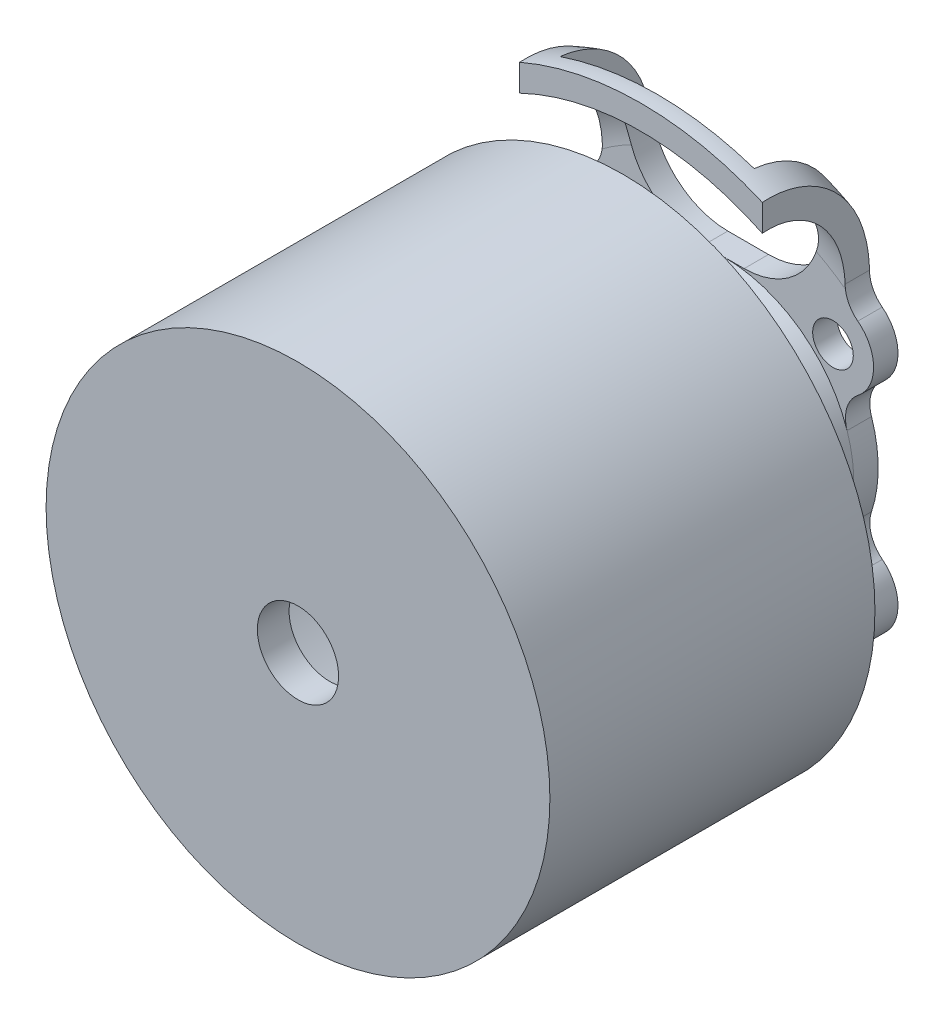
SolidWorks part; units mm, degrees
material "AISI 1020 Steel, Cold Rolled"
ref_plane "Front Plane" through (0, 0, 0) normal (0, 0, 1) x (1, 0, 0)
ref_plane "Top Plane" through (0, 0, 0) normal (0, 1, 0) x (1, 0, 0)
ref_plane "Right Plane" through (0, 0, 0) normal (1, 0, 0) x (0, 0, -1)
sketch "Sketch1" plane through (0, 0, 0) normal (1, 0, 0) x (0, 0, -1)
  line L1 (0, 15.5) -> (20, 15.5)
  line L3 (20, 0) -> (0, 0) construction
  line L4 (20, 2.5) -> (0, 2.5) construction
  line L5 (0, 15.5) -> (0, 2.5)
  line L6 (0, 2.5) -> (1.95, 2.5)
  line L7 (1.95, 2.5) -> (1.95, 13.5)
  line L8 (1.95, 13.5) -> (18.05, 13.5)
  line L9 (18.05, 13.5) -> (18.05, 2.5)
  line L10 (18.05, 2.5) -> (20, 2.5)
  line L11 (20, 6.5) -> (20, 15.5)
  line L12 (20, 2.5) -> (27.7, 2.5)
  line L13 (27.7, 2.5) -> (27.7, 12.5)
  line L14 (27.7, 18.75) -> (-25.5, 18.75) construction
  line L18 (20, 6.5) -> (26.2, 8)
  line L19 (26.2, 8) -> (26.2, 12.5)
  line L20 (21.1007, 18.7402) -> (21.1007, 17.2402)
  line L21 (26.2, 8) -> (27.7, 8) construction
  line L22 (10, 13.5) -> (10, 15.5) construction
  arc A2 (27.7, 12.5) -> (21.1007, 18.7402) centre (21.45, 12.5) ccw
  arc A3 (26.2, 12.5) -> (21.1007, 17.2402) centre (21.4471, 12.5) ccw
  dimension "D10" = 1.5
  dimension "D1" = 20
  dimension "D2" = 15.5
  dimension "D3" = 2.5
  dimension "D4" = 12.5
  dimension "D5" = 27.7
  dimension "D6" = 18.75
  dimension "D7" = 53.2
  dimension "D8" = 6.5
  dimension "D9" = 8
  dimension "D11" = 16.1
  dimension "D12" = 11
revolve "Revolve1" add sketch "Sketch1" angle 360 about L3
sketch "Sketch2" plane through (0, 0, -27.7) normal (0, 0, -1) x (-1, 0, 0)
  line L0 (-5.9675, 23.4161) -> (-5.9675, 12.7175)
  line L1 (-6.7175, -6.7175) -> (6.7175, -6.7175) construction
  line L2 (-6.7175, -6.7175) -> (-6.7175, 6.7175) construction
  line L3 (-6.7175, 6.7175) -> (6.7175, 6.7175) construction
  line L4 (6.7175, -6.7175) -> (6.7175, 6.7175) construction
  line L5 (-6.7175, -6.7175) -> (6.7175, 6.7175) construction
  line L6 (-6.7175, 6.7175) -> (6.7175, -6.7175) construction
  line L7 (-5.9675, 23.4161) -> (5.9675, 23.4161)
  line L8 (5.9675, 23.4161) -> (5.9675, 12.7175)
  line L9 (0, 0) -> (0, 23.4161) construction
  line L10 (1.25, 8) -> (-1.25, 8)
  line L11 (-7.4675, 23.4161) -> (-7.4675, 10.2795)
  line L12 (7.4675, 23.4161) -> (7.4675, 10.2795)
  line L13 (7.4675, 23.4161) -> (5.9675, 23.4161) construction
  line L14 (6.7175, 6.7175) -> (6.7175, 23.4161) construction
  line L15 (-5.9675, 23.4161) -> (-7.4675, 23.4161) construction
  circle A0 centre (0, 0) radius 9.5 construction
  circle A1 centre (0, 0) radius 8 construction
  circle A2 centre (0, 0) radius 12.5 construction
  circle A3 centre (-6.7175, 6.7175) radius 1.25
  circle A4 centre (6.7175, 6.7175) radius 1.25
  circle A5 centre (6.7175, -6.7175) radius 1.25
  circle A6 centre (-6.7175, -6.7175) radius 1.25
  circle A7 centre (6.7175, 6.7175) radius 2.5 construction
  circle A8 centre (6.7175, -6.7175) radius 2.5 construction
  circle A9 centre (-6.7175, -6.7175) radius 2.5 construction
  circle A11 centre (-6.7175, 6.7175) radius 2.5 construction
  arc A17 (-5.9675, 12.7175) -> (-1.25, 8) centre (-1.25, 12.7175) ccw
  arc A19 (5.9675, 12.7175) -> (1.25, 8) centre (1.25, 12.7175) cw
  arc A22 (-7.4675, 23.4161) -> (7.4675, 23.4161) centre (0, -0.8704) ccw
  arc A25 (8.2453, 8.6964) -> (8.2548, 4.746) centre (6.7175, 6.7175) cw
  arc A26 (7.5877, 2.5351) -> (7.5877, -2.5351) centre (0, 0) cw
  arc A27 (8.2548, -4.746) -> (4.746, -8.2548) centre (6.7175, -6.7175) cw
  arc A28 (2.5351, -7.5877) -> (-2.5351, -7.5877) centre (0, 0) cw
  arc A29 (-4.746, -8.2548) -> (-8.2548, -4.746) centre (-6.7175, -6.7175) cw
  arc A30 (-8.2453, 8.6964) -> (-8.2548, 4.746) centre (-6.7175, 6.7175) ccw
  arc A31 (-7.5877, 2.5351) -> (-7.5877, -2.5351) centre (0, 0) ccw
  arc A32 (-8.2453, 8.6964) -> (-7.4675, 10.2795) centre (-9.4675, 10.2795) ccw
  arc A33 (-7.5877, 2.5351) -> (-8.2548, 4.746) centre (-9.4846, 3.1689) ccw
  arc A34 (-8.2548, -4.746) -> (-7.5877, -2.5351) centre (-9.4846, -3.1689) ccw
  arc A35 (-4.746, -8.2548) -> (-2.5351, -7.5877) centre (-3.1689, -9.4846) cw
  arc A36 (2.5351, -7.5877) -> (4.746, -8.2548) centre (3.1689, -9.4846) cw
  arc A37 (8.2548, -4.746) -> (7.5877, -2.5351) centre (9.4846, -3.1689) cw
  arc A38 (7.5877, 2.5351) -> (8.2548, 4.746) centre (9.4846, 3.1689) cw
  arc A39 (8.2453, 8.6964) -> (7.4675, 10.2795) centre (9.4675, 10.2795) cw
  point P47 (7.4675, 9.1024)
  point P48 (-7.4675, 9.1024)
  point P50 (-7.4675, 9.1024)
  point P53 (-6.7972, 4.2188)
  point P56 (-6.7972, -4.2188)
  point P59 (-4.2188, -6.7972)
  point P62 (4.2188, -6.7972)
  point P65 (6.7972, -4.2188)
  point P68 (6.7972, 4.2188)
  point P71 (7.4675, 9.1024)
  dimension "D1" = 19
  dimension "D2" = 16
  dimension "D3" = 25
  dimension "D4" = 2.5
  dimension "D5" = 5
  dimension "D7" = 2
  dimension "D6" = 1.5
  dimension "D8" = 2.5
extrude "Cut-Extrude1" cut sketch "Sketch2" against normal offset from surface (5.5993 mm away) 1 up to face at (-17.2402, 0, -21.1007)
sketch "Sketch3" plane through (0, 0, -21.1007) normal (0, 0, 1) x (1, 0, 0)
  line L0 (-7.4675, 17.1988) -> (-7.4675, 0) construction
  line L1 (-7.4675, 0) -> (7.4675, 0) construction
  line L2 (7.4675, 0) -> (7.4675, 17.1988) construction
  line L4 (7.4675, 15.503) -> (7.4675, 17.1618) construction
  line L5 (7.4675, 17.1988) -> (7.4675, 15.503)
  line L6 (-7.4675, 17.1988) -> (-7.4675, 15.503)
  arc A0 (7.4675, 17.1988) -> (-7.4675, 17.1988) centre (0, 0) cw
  arc A1 (-7.4675, 15.503) -> (7.4675, 15.503) centre (0, 0) ccw
  arc A2 (5.9675, 16.1398) -> (-5.9675, 16.1398) centre (0, 0) ccw construction
  point P5 (0, 0)
  dimension "D1" = 18.75
extrude "Cut-Extrude2" cut sketch "Sketch3" against normal up to next
move or copy body "Body-Move/Copy1" [suppressed] bodies to move or copy 103 parameters "D1"=0, "D2"=0, "D3"=0
